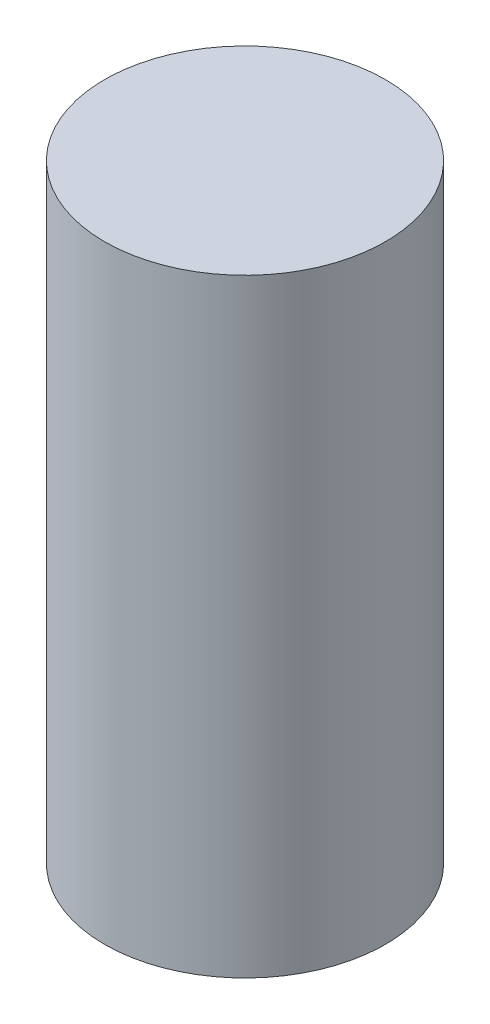
SolidWorks part; units mm, degrees
material "1060 Alloy"
ref_plane "Front Plane" through (0, 0, 0) normal (0, 0, 1) x (1, 0, 0)
ref_plane "Top Plane" through (0, 0, 0) normal (0, 1, 0) x (1, 0, 0)
ref_plane "Right Plane" through (0, 0, 0) normal (1, 0, 0) x (0, 0, -1)
sketch "Sketch1" plane through (0, 0, 0) normal (0, 1, 0) x (1, 0, 0)
  circle A0 centre (-12.5992, 5.1225) radius 3
extrude "Boss-Extrude1" add sketch "Sketch1" along normal blind 13
